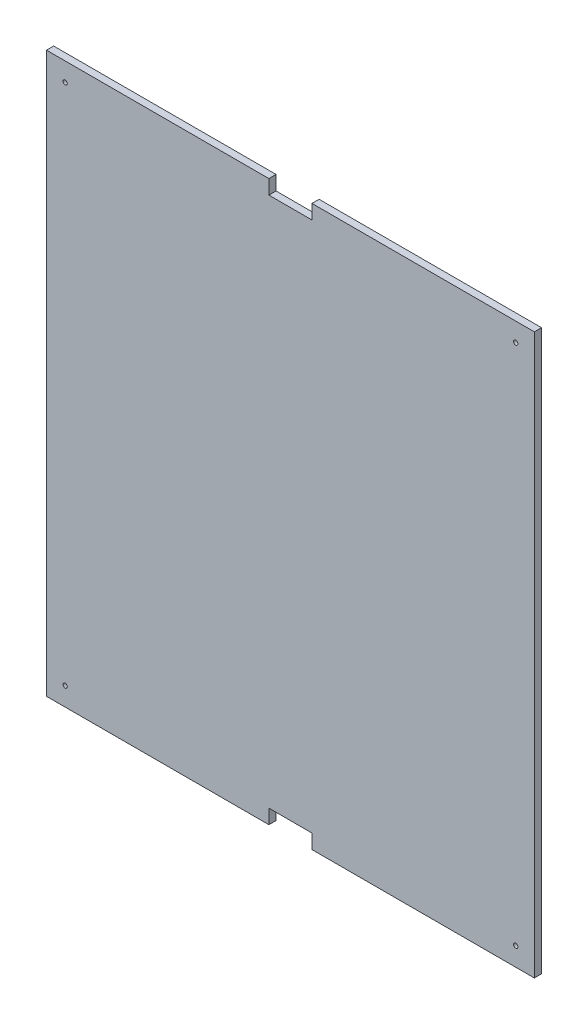
SolidWorks part; units mm, degrees
material "ABS"
ref_plane "Alzado" through (0, 0, 0) normal (0, 0, 1) x (1, 0, 0)
ref_plane "Planta" through (0, 0, 0) normal (0, 1, 0) x (1, 0, 0)
ref_plane "Vista lateral" through (0, 0, 0) normal (1, 0, 0) x (0, 0, -1)
sketch "Croquis1" plane through (0, 0, 0) normal (0, 0, 1) x (1, 0, 0)
  line L0 (-108.3974, -340.464) -> (46.6026, -340.464)
  line L1 (76.6026, -340.464) -> (231.6026, -340.464)
  line L2 (-108.3974, 49.536) -> (-108.3974, -340.464)
  line L3 (231.6026, 49.536) -> (76.6026, 49.536)
  line L4 (231.6026, 49.536) -> (231.6026, -340.464)
  line L5 (-108.3974, 49.536) -> (46.6026, 49.536)
  line L6 (46.6026, -340.464) -> (46.6026, -330.464)
  line L7 (46.6026, -330.464) -> (76.6026, -330.464)
  line L8 (76.6026, -340.464) -> (76.6026, -330.464)
  line L10 (46.6026, 49.536) -> (46.6026, 39.536)
  line L11 (46.6026, 39.536) -> (76.6026, 39.536)
  line L12 (76.6026, 49.536) -> (76.6026, 39.536)
  circle A0 centre (-95.3974, -327.464) radius 1.5
  circle A1 centre (218.6026, -327.464) radius 1.5
  circle A2 centre (218.6026, 36.536) radius 1.5
  circle A3 centre (-95.3974, 36.536) radius 1.5
  dimension "D1" = 340
  dimension "D2" = 390
  dimension "D4" = 13
  dimension "D5" = 13
  dimension "D7" = 13
  dimension "D10" = 13
  dimension "D11" = 30
  dimension "D12" = 10
  dimension "D13" = 10
  dimension "D14" = 30
  dimension "D15" = 155
  dimension "D16" = 155
extrude "Saliente-Extruir1" add sketch "Croquis1" along normal blind 5
